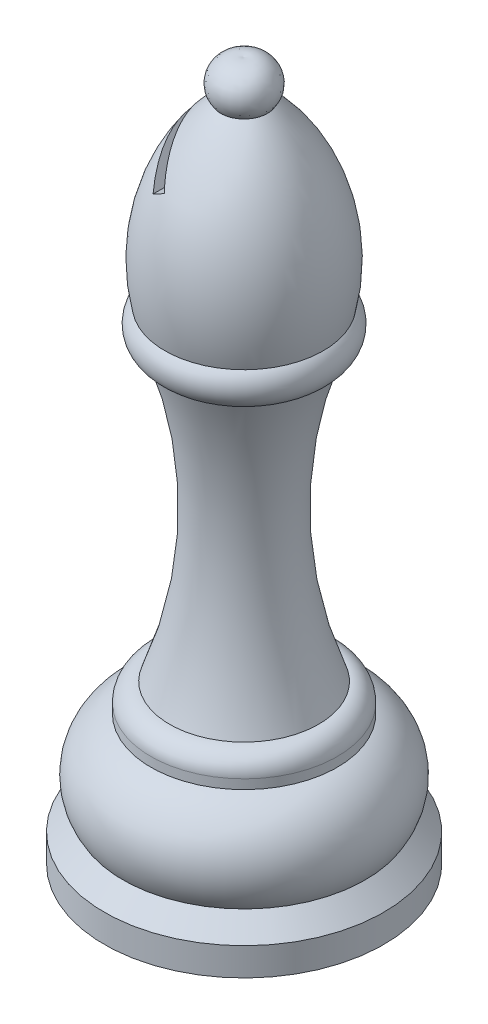
SolidWorks part; units mm, degrees
ref_plane "Front Plane" through (0, 0, 0) normal (0, 0, 1) x (1, 0, 0)
ref_plane "Top Plane" through (0, 0, 0) normal (0, 1, 0) x (1, 0, 0)
ref_plane "Right Plane" through (0, 0, 0) normal (1, 0, 0) x (0, 0, -1)
sketch "Sketch1" plane through (0, 0, 0) normal (0, 0, 1) x (1, 0, 0)
  line L0 (0, 0) -> (0, 75) construction
  line L1 (0, 0) -> (-15, 0)
  line L2 (0, 0) -> (0, 3)
  line L3 (0, 3) -> (0, 5)
  line L4 (0, 5) -> (0, 13.97)
  line L5 (0, 13.97) -> (0, 14.97)
  line L6 (0, 14.97) -> (0, 16.97)
  line L8 (-15, 3) -> (-15, 0)
  line L10 (-13, 5) -> (-15, 3)
  line L13 (-10, 14.97) -> (-10, 13.97)
  line L15 (0, 16.97) -> (0, 47.99)
  line L17 (0, 47.99) -> (0, 51.93)
  line L19 (0, 51.93) -> (0, 70.99)
  line L21 (0, 70.99) -> (0, 75)
  arc A0 (-13, 5) -> (-10, 13.97) centre (-7.9981, 8.3138) cw
  arc A1 (-10, 14.97) -> (-8, 16.97) centre (-8, 14.97) cw
  arc A2 (-7.5, 47.99) -> (-8, 16.97) centre (-49.9864, 33.1608) cw
  arc A3 (-7.5, 47.99) -> (-8.5, 51.93) centre (-6.9565, 50.2249) cw
  arc A4 (-8.5, 51.93) -> (-2.5, 70.99) centre (11.0262, 56.2576) cw
  arc A5 (-2.5, 70.99) -> (0, 75) centre (-0.5567, 72.5628) cw
  dimension "D10" = 6
  dimension "D13" = 45
  dimension "D16" = 2.3
  dimension "D19" = 20
  dimension "D20" = 2.5
  dimension "D1" = 75
  dimension "D2" = 15
  dimension "D3" = 3
  dimension "D4" = 2
  dimension "D5" = 8.97
  dimension "D6" = 1
  dimension "D7" = 2
  dimension "D8" = 13
  dimension "D9" = 10
  dimension "D11" = 31.02
  dimension "D12" = 7.5
  dimension "D14" = 3.94
  dimension "D15" = 8.5
  dimension "D17" = 19.06
  dimension "D18" = 2.5
revolve "Revolve1" add sketch "Sketch1" angle 360 about L0
sketch "Sketch2" plane through (0, 0, 0) normal (0, 0, 1) x (1, 0, 0)
  line L0 (-4.2497, 69.1668) -> (-1.7497, 64.8367)
  line L1 (-1.7497, 64.8367) -> (-3.0487, 64.0867)
  line L2 (-3.0487, 64.0867) -> (-5.2439, 67.8888)
  line L4 (0, 51.93) -> (0, 79.8709) construction
  line L5 (8.5, 51.93) -> (-8.5, 51.93) construction
  line L6 (-4.6311, 69.887) -> (-4.2497, 69.1668)
  line L7 (-5.2439, 67.8888) -> (-5.8238, 68.8932)
  line L8 (-5.8238, 68.8932) -> (-4.6311, 69.887)
  arc A0 (-2.5, 70.99) -> (-8.5, 51.93) centre (11.0262, 56.2576) ccw construction
  dimension "D1" = 5
  dimension "D2" = 30
  dimension "D3" = 1.5
extrude "Cut-Extrude1" cut sketch "Sketch2" against normal through all both and the other way through all
